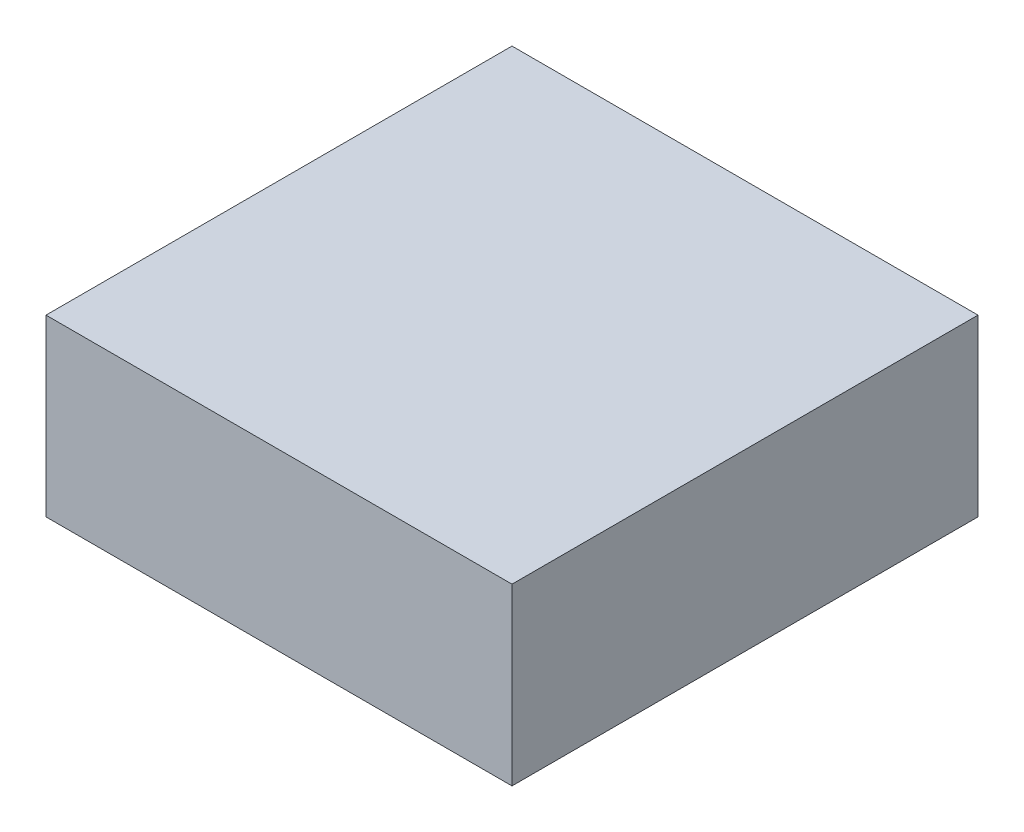
SolidWorks part; units mm, degrees
ref_plane "Front Plane" through (0, 0, 0) normal (0, 0, 1) x (1, 0, 0)
ref_plane "Top Plane" through (0, 0, 0) normal (0, 1, 0) x (1, 0, 0)
ref_plane "Right Plane" through (0, 0, 0) normal (1, 0, 0) x (0, 0, -1)
sketch "Sketch1" plane through (0, 0, 0) normal (0, 1, 0) x (1, 0, 0)
  line L1 (0, 0) -> (-50.8, 0)
  line L2 (0, 0) -> (0, 50.8)
  line L3 (0, 50.8) -> (-50.8, 50.8)
  line L4 (-50.8, 0) -> (-50.8, 50.8)
  dimension "D1" = 50.8
  dimension "D2" = 50.8
extrude "Boss-Extrude1" add sketch "Sketch1" along normal blind 19.05
